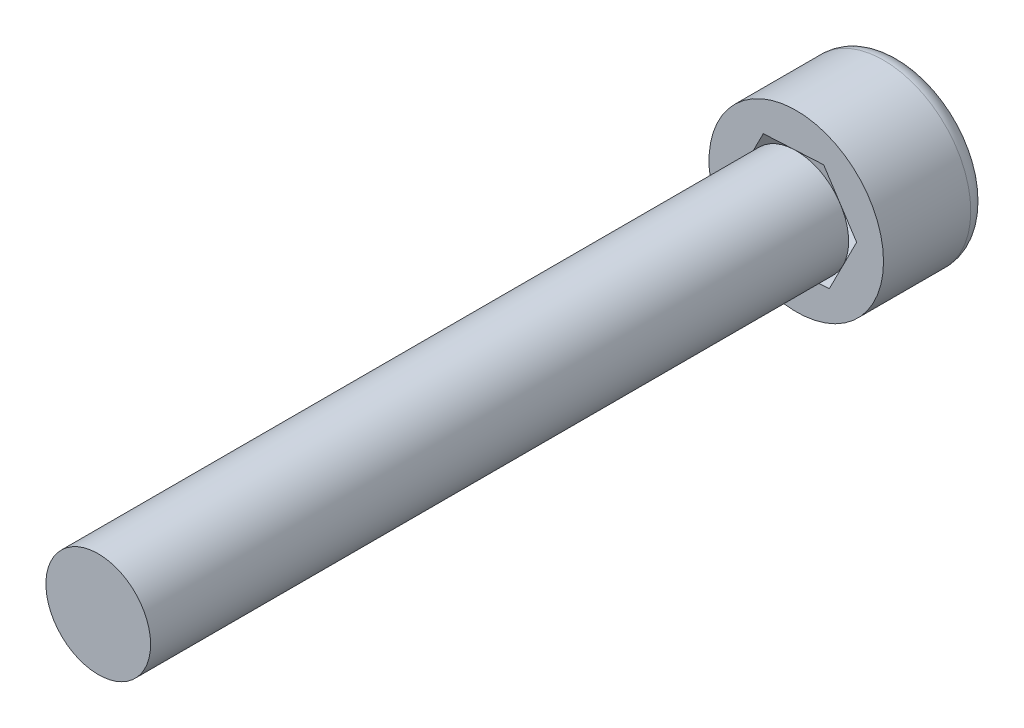
SolidWorks part; units mm, degrees
ref_plane "Front Plane" through (0, 0, 0) normal (0, 0, 1) x (1, 0, 0)
ref_plane "Top Plane" through (0, 0, 0) normal (0, 1, 0) x (1, 0, 0)
ref_plane "Right Plane" through (0, 0, 0) normal (1, 0, 0) x (0, 0, -1)
sketch "Sketch1" plane through (0, 0, 0) normal (0, 0, 1) x (1, 0, 0)
  circle A0 centre (0, 0) radius 2.5
  dimension "D1" = 5
extrude "Boss-Extrude1" add sketch "Sketch1" along normal blind 3
sketch "Sketch2" plane through (0, 0, 3) normal (0, 0, 1) x (1, 0, 0)
  circle A0 centre (0, 0) radius 1.5
  dimension "D1" = 3
extrude "Boss-Extrude2" add sketch "Sketch2" along normal blind 20
sketch "Sketch3" plane through (0, 0, 0) normal (0, 0, -1) x (-1, 0, 0)
  line L1 (0.7845, -1.5442) -> (1.7296, -0.0927)
  line L2 (1.7296, -0.0927) -> (0.9451, 1.4515)
  line L3 (0.9451, 1.4515) -> (-0.7845, 1.5442)
  line L4 (-0.7845, 1.5442) -> (-1.7296, 0.0927)
  line L5 (-1.7296, 0.0927) -> (-0.9451, -1.4515)
  line L6 (-0.9451, -1.4515) -> (0.7845, -1.5442)
  circle A0 centre (0, 0) radius 1.5 construction
  dimension "D1" = 3
extrude "Cut-Extrude1" cut sketch "Sketch3" against normal blind 3
fillet "Fillet1" radius 0.5 1 edges at (2.5, 0, 0)
